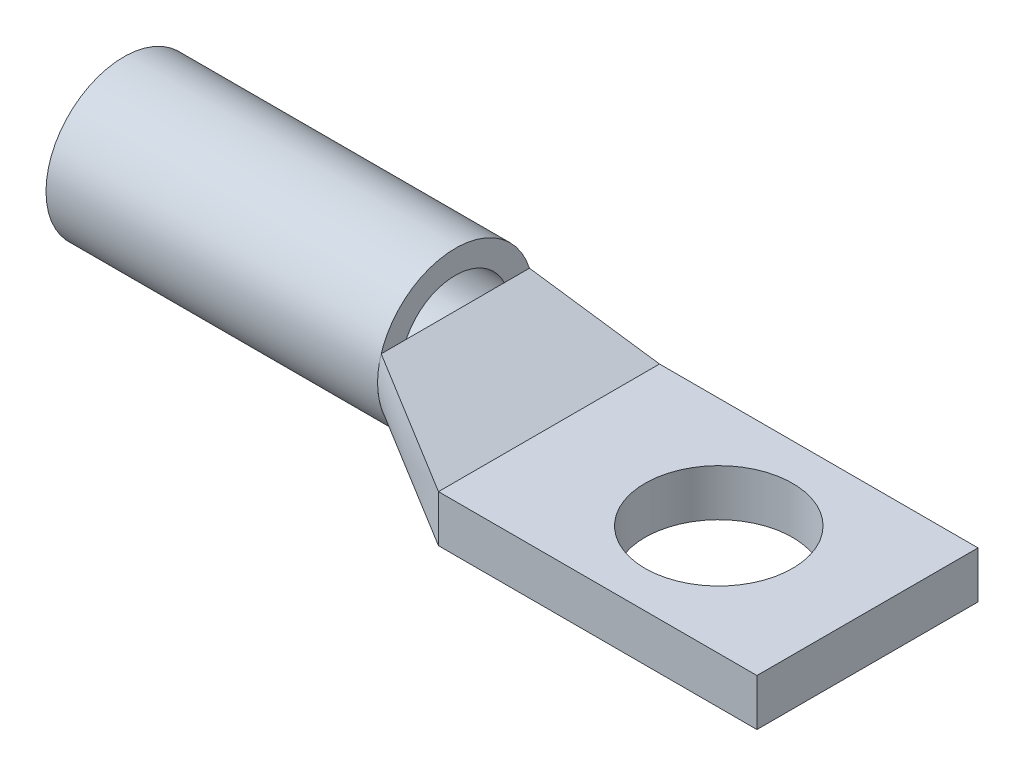
SolidWorks part; units mm, degrees
ref_plane "Front" through (0, 0, 0) normal (0, 0, 1) x (1, 0, 0)
ref_plane "Top" through (0, 0, 0) normal (0, 1, 0) x (1, 0, 0)
ref_plane "Right" through (0, 0, 0) normal (1, 0, 0) x (0, 0, -1)
sketch "Sketch1" plane through (0, 0, 0) normal (0, 1, 0) x (1, 0, 0)
  line L1 (10.08, 7.493) -> (-11.51, 7.493)
  line L2 (10.08, 7.493) -> (10.08, -7.493)
  line L3 (10.08, -7.493) -> (-11.51, -7.493)
  line L4 (-11.51, 7.493) -> (-11.51, -7.493)
  line L5 (-0.715, -7.493) -> (-0.715, 7.493) construction
  line L6 (10.08, 0) -> (-11.51, 0) construction
  circle A1 centre (0, 0) radius 5
  dimension "D1" = 10
  dimension "D3" = 21.59
  dimension "D4" = 10.08
  dimension "D2" = 14.986
extrude "Boss-Extrude1" add sketch "Sketch1" along normal blind 3.175
ref_plane "Plane1" through (-17.86, 0, 0) normal (-1, 0, 0) x (0, 0, 1)
ref_plane "Plane2" through (-40.339, 0, 0) normal (-1, 0, 0) x (0, 0, 1)
sketch "Sketch2" plane through (-40.339, 0, 0) normal (-1, 0, 0) x (0, 0, 1)
  circle A0 centre (0, 5.2705) radius 5.2705
  dimension "D1" = 10.541
extrude "Extrude-Thin1" add sketch "Sketch2" against normal up to surface (22.479 mm away) separate body thin contours A0 up to plane "Plane1" thin type one direction reverse wall 1.5875
sketch "Sketch5" plane through (-11.51, 0, 0) normal (-1, 0, 0) x (0, 0, 1)
  line L14 (-7.493, 0) -> (7.493, 0)
  line L15 (7.493, 0) -> (7.493, 3.175)
  line L16 (7.493, 3.175) -> (-7.493, 3.175)
  line L17 (-7.493, 3.175) -> (-7.493, 0)
  line L18 (-7.493, 0) -> (7.493, 0)
  line L19 (7.493, 0) -> (7.493, 3.175)
  line L20 (7.493, 3.175) -> (-7.493, 3.175)
  line L21 (-7.493, 3.175) -> (-7.493, 0)
  dimension "D1" = 0
sketch "Sketch7" plane through (-17.86, 0, 0) normal (1, 0, 0) x (0, 0, -1)
  line L0 (-5.0257, 6.858) -> (-5.0257, 3.683) construction
  line L1 (5.0257, 6.858) -> (5.0257, 3.683) construction
  line L2 (-5.0257, 6.858) -> (5.0257, 6.858)
  circle A0 centre (0, 5.2705) radius 5.2705 construction
  arc A1 (-5.0257, 3.683) -> (5.0257, 3.683) centre (0, 5.2705) ccw
  arc A2 (-5.0257, 3.683) -> (-5.0257, 6.858) centre (0, 5.2705) cw
  arc A3 (5.0257, 6.858) -> (5.0257, 3.683) centre (0, 5.2705) cw
  dimension "D1" = 3.175
surface "Surface-Loft2"
sketch3d "3DSketch1"
  line L0 (-40.339, 5.2705, 0) -> (-17.86, 5.2705, 0)
  line L1 (-17.86, 5.2705, 0) -> (-40.339, 5.2705, 0) construction
